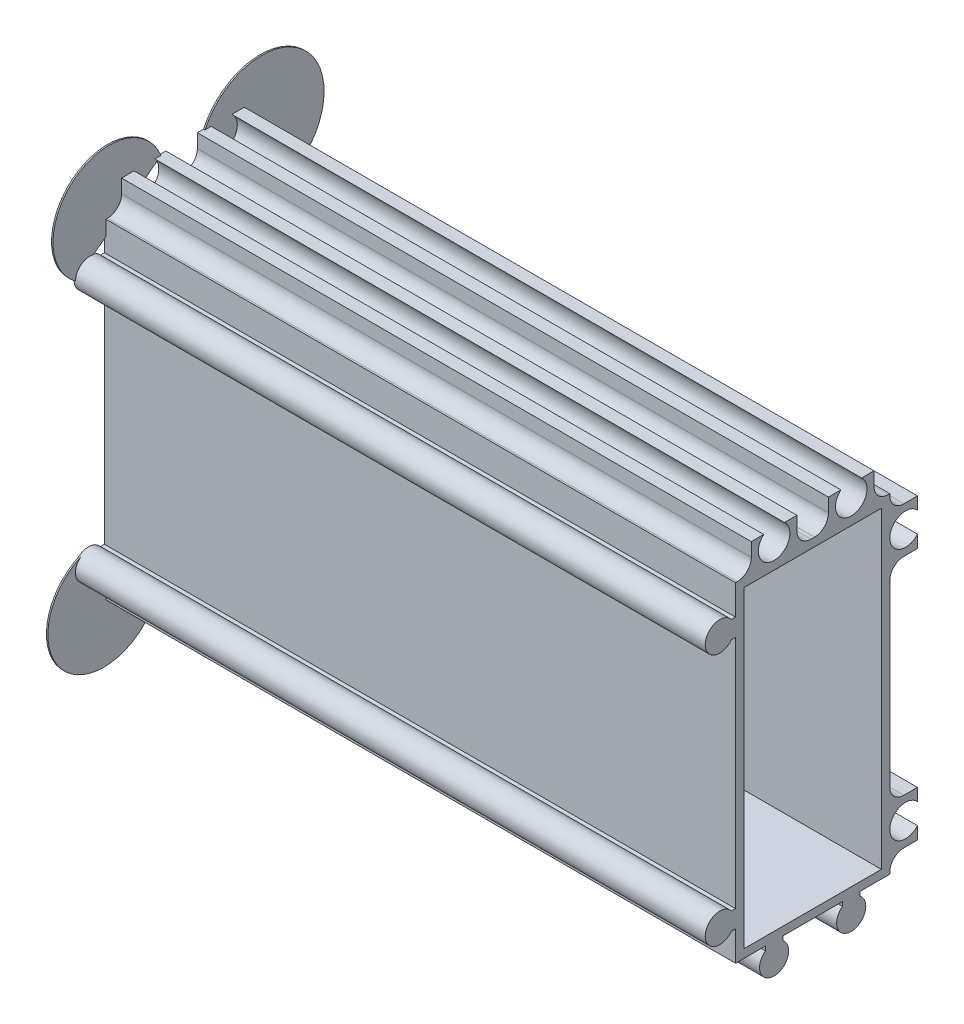
SolidWorks part; units mm, degrees
ref_plane "Спереди" through (0, 0, 0) normal (0, 0, 1) x (1, 0, 0)
ref_plane "Сверху" through (0, 0, 0) normal (0, 1, 0) x (1, 0, 0)
ref_plane "Справа" through (0, 0, 0) normal (1, 0, 0) x (0, 0, -1)
ref_plane "Плоскость4" through (90, 0, 0) normal (1, 0, 0) x (0, 0, -1)
sketch "Эскиз1" plane through (90, 0, 0) normal (1, 0, 0) x (0, 0, -1)
  line L0 (6.75, -24.0938) -> (6.75, 19.25)
  line L1 (6.75, 19.25) -> (-11.5938, 19.25)
  line L2 (-11.5938, 16.75) -> (-11, 16.75)
  line L3 (-11, 16.75) -> (-11, -16.75)
  line L4 (-11, -16.75) -> (-11.5938, -16.75)
  line L5 (-11.5938, -19.25) -> (-11, -19.25)
  line L6 (-11, -19.25) -> (-11, -23.5)
  line L7 (-11, -23.5) -> (-6.75, -23.5)
  line L8 (-6.75, -23.5) -> (-6.75, -24.0938)
  line L9 (-4.25, -24.0938) -> (-4.25, -23.5)
  line L10 (-4.25, -23.5) -> (4.25, -23.5)
  line L11 (4.25, -23.5) -> (4.25, -24.0938)
  arc A0 (-11.5938, 19.25) -> (-11.5938, 16.75) centre (-13.25, 18) ccw
  arc A1 (-11.5938, -16.75) -> (-11.5938, -19.25) centre (-13.25, -18) ccw
  arc A2 (-6.75, -24.0938) -> (-4.25, -24.0938) centre (-5.5, -25.75) ccw
  arc A3 (4.25, -24.0938) -> (6.75, -24.0938) centre (5.5, -25.75) ccw
extrude "Бобышка-Вытянуть1" add sketch "Эскиз1" against normal blind 90
sketch "Эскиз2" plane through (0, 19.25, 0) normal (0, 1, 0) x (-1, 0, 0)
  line L0 (-90, -6.75) -> (-90, 11)
  line L1 (-90, 11) -> (0, 11)
  line L2 (0, 11) -> (0, -6.75)
  line L3 (0, -6.75) -> (-90, -6.75)
extrude "Бобышка-Вытянуть2" add sketch "Эскиз2" along normal blind 8.2
sketch "Эскиз3" plane through (0, 0, -6.75) normal (0, 0, -1) x (-1, 0, 0)
  line L0 (0, -23.5) -> (-90, -23.5)
  line L1 (-90, -23.5) -> (-90, 27.45)
  line L2 (-90, 27.45) -> (0, 27.45)
  line L3 (0, 27.45) -> (0, -23.5)
extrude "Бобышка-Вытянуть3" add sketch "Эскиз3" along normal blind 8.2
sketch "Эскиз4" plane through (0, 0, 0) normal (-1, 0, 0) x (0, 0, 1)
  line L0 (-14.95, -14.75) -> (-11, -14.75)
  line L1 (-11, -14.75) -> (-11, 14.75)
  line L2 (-11, 14.75) -> (-14.95, 14.75)
  line L3 (-14.95, 14.75) -> (-14.95, -14.75)
extrude "Вырез-Вытянуть1" cut sketch "Эскиз4" against normal through all
sketch "Эскиз5" plane through (0, 0, 0) normal (-1, 0, 0) x (0, 0, 1)
  line L0 (-14.95, 27.45) -> (-14.95, 21.25)
  line L1 (-14.95, 21.25) -> (-11, 21.25)
  line L2 (-11, 21.25) -> (-11, 27.45)
  line L3 (-11, 27.45) -> (-14.95, 27.45)
extrude "Вырез-Вытянуть2" cut sketch "Эскиз5" against normal through all
sketch "Эскиз6" plane through (0, 0, 0) normal (-1, 0, 0) x (0, 0, 1)
  line L0 (-11, 27.45) -> (-11, 23.5)
  line L1 (-11, 23.5) -> (-8.75, 23.5)
  line L2 (-8.75, 23.5) -> (-8.75, 27.45)
  line L3 (-8.75, 27.45) -> (-11, 27.45)
extrude "Вырез-Вытянуть3" cut sketch "Эскиз6" against normal through all
sketch "Эскиз7" plane through (0, 0, 0) normal (-1, 0, 0) x (0, 0, 1)
  line L0 (-2.25, 27.45) -> (-2.25, 23.5)
  line L1 (-2.25, 23.5) -> (2.25, 23.5)
  line L2 (2.25, 23.5) -> (2.25, 27.45)
  line L3 (2.25, 27.45) -> (-2.25, 27.45)
extrude "Вырез-Вытянуть4" cut sketch "Эскиз7" against normal through all
sketch "Эскиз8" plane through (0, 0, 0) normal (-1, 0, 0) x (0, 0, 1)
  line L0 (11, 27.45) -> (8.75, 27.45)
  line L1 (8.75, 27.45) -> (8.75, 23.5)
  line L2 (8.75, 23.5) -> (11, 23.5)
  line L3 (11, 23.5) -> (11, 27.45)
extrude "Вырез-Вытянуть5" cut sketch "Эскиз8" against normal through all
sketch "Эскиз9" plane through (0, 0, 0) normal (-1, 0, 0) x (0, 0, 1)
  line L0 (-14.95, -23.5) -> (-11, -23.5)
  line L1 (-11, -23.5) -> (-11, -21.25)
  line L2 (-11, -21.25) -> (-14.95, -21.25)
  line L3 (-14.95, -21.25) -> (-14.95, -23.5)
extrude "Вырез-Вытянуть6" cut sketch "Эскиз9" against normal through all
sketch "Эскиз10" plane through (90, 0, 0) normal (1, 0, 0) x (0, 0, -1)
  line L0 (9.8, 22.3) -> (-9.8, 22.3)
  line L1 (-9.8, 22.3) -> (-9.8, -22.3)
  line L2 (-9.8, -22.3) -> (9.8, -22.3)
  line L3 (9.8, -22.3) -> (9.8, 22.3)
  line L4 (-11, 16.75) -> (-11, -16.75) construction
  line L8 (11, -14.75) -> (11, 14.75) construction
  line L9 (2.25, 23.5) -> (-2.25, 23.5) construction
  line L10 (-4.25, -23.5) -> (4.25, -23.5) construction
  dimension "D1" = 1.2
  dimension "D2" = 1.2
  dimension "D3" = 1.2
  dimension "D4" = 1.2
extrude "Вырез-Вытянуть7" cut sketch "Эскиз10" against normal blind 86.2
hole_wizard "Диаметр отверстия Ø2.5 (2.5)1" positions "Эскиз12" profile "Эскиз11" hole size "Ø2.5" standard "Ansi Metric"
sketch "Эскиз12" plane through (90, 0, 0) normal (1, 0, 0) x (0, 0, -1)
  point P0 (5.5, -25.75)
  point P1 (-13.25, -18)
  point P2 (-5.5, -25.75)
  point P3 (-13.25, 18)
sketch "Эскиз11" plane through (90, -25.75, -5.5) normal (0, 1, 0) x (0, 0, -1)
  line L0 (0, 0) -> (0, 90)
  line L1 (0, 90) -> (1.25, 90)
  line L2 (1.25, 90) -> (1.25, 0)
  line L5 (1.25, 0) -> (0, 0)
  line L11 (0, -6.35) -> (0, 107.95) construction
  dimension "Диаметр сквозного отверстия" = 2.5
  dimension "Глубина сквозного отверстия" = 90
hole_wizard "Диаметр отверстия Ø4.5 (4.5)1" positions "Эскиз14" profile "Эскиз13" hole size "Ø4.5" standard "Ansi Metric"
sketch "Эскиз14" plane through (0, 0, 0) normal (-1, 0, 0) x (0, 0, 1)
  point P0 (-13.25, -18)
  point P1 (-13.25, 18)
  point P2 (-5.5, 25.75)
  point P3 (5.5, 25.75)
sketch "Эскиз13" plane through (0, -18, -13.25) normal (0, 1, 0) x (0, 0, 1)
  line L0 (0, 0) -> (0, 90)
  line L1 (0, 90) -> (2.25, 90)
  line L2 (2.25, 90) -> (2.25, 0)
  line L5 (2.25, 0) -> (0, 0)
  line L11 (0, -6.35) -> (0, 107.95) construction
  dimension "Диаметр сквозного отверстия" = 4.5
  dimension "Глубина сквозного отверстия" = 90
hole_wizard "Диаметр отверстия Ø8.3 (8.3)1" [suppressed] positions "Эскиз16" profile "Эскиз15" hole size "Ø8.3" standard "Ansi Metric"
sketch "Эскиз16" plane through (0, 0, 0) normal (-1, 0, 0) x (0, 0, 1)
  point P0 (0, 0)
sketch "Эскиз15" plane through (0, 0, 0) normal (0, 1, 0) x (0, 0, 1)
  line L0 (0, 0) -> (0, 3.2)
  line L1 (0, 3.2) -> (4.15, 3.2)
  line L2 (4.15, 3.2) -> (4.15, 0)
  line L5 (4.15, 0) -> (0, 0)
  line L10 (0, 3.2) -> (-4.15, 3.2) construction
  line L11 (0, -6.35) -> (0, 107.95) construction
  dimension "Диаметр отверстия" = 8.3
  dimension "Глубина отверстия" = 3.2
  dimension "Угол заточки сверла" = 180
fillet "Скругление1" radius 2 1 edges at (45, 23.5, 8.75)
fillet "Скругление2" radius 2 7 edges at (45, -21.25, -11) (45, -14.75, -11) (45, 14.75, -11) (45, 21.25, -11) (45, 23.5, -8.75) (45, 23.5, -2.25) (45, 23.5, 2.25)
sketch "Эскиз17" plane through (90, 0, 0) normal (1, 0, 0) x (0, 0, -1)
  circle A0 centre (5.5, -25.75) radius 1.25 construction
  circle A1 centre (-5.5, -25.75) radius 1.25 construction
  circle A2 centre (-13.25, -18) radius 1.25 construction
  circle A3 centre (-13.25, 18) radius 1.25 construction
  circle A4 centre (5.5, -25.75) radius 1.25
  circle A5 centre (-5.5, -25.75) radius 1.25
  circle A6 centre (-13.25, -18) radius 1.25
  circle A7 centre (-13.25, 18) radius 1.25
extrude "Бобышка-Вытянуть4" add sketch "Эскиз17" against normal blind 90
sketch "Эскиз18" [suppressed] plane through (0, 0, 0) normal (-1, 0, 0) x (0, 0, 1)
  circle A0 centre (0, 0) radius 4.15 construction
  circle A1 centre (0, 0) radius 4.15
extrude "Вырез-Вытянуть8" [suppressed] cut sketch "Эскиз18" against normal blind 100
sketch "Эскиз19" plane through (0, 0, 0) normal (-1, 0, 0) x (0, 0, 1)
  line L0 (11, -23.5) -> (-11, 23.25) construction
  line L1 (-11, -23.5) -> (11, 23.5157) construction
  line L2 (11, 23.5) -> (11, 19.25) construction
  line L3 (0, 0) -> (11, 0) construction
  line L4 (11, 16.75) -> (11, -16.75) construction
  line L5 (-4.0261, 27.45) -> (-2.25, 27.45) construction
  line L6 (-14.95, 14.75) -> (-14.95, 16.5261) construction
  line L7 (2.25, 27.45) -> (4.0261, 27.45) construction
  line L8 (-14.95, -16.5261) -> (-14.95, -14.75) construction
  line L9 (-14.95, 15.638) -> (-3.138, 27.45)
  line L10 (15.325, 18) -> (3.138, 27.45)
  line L11 (14.6082, -16.4313) -> (4.1213, -27.3007)
  line L12 (-5.5, -27.825) -> (-14.95, -15.638)
  arc A0 (-3.138, 27.45) -> (-14.95, 15.638) centre (-11.2222, 23.7222) ccw
  arc A1 (15.325, 18) -> (3.138, 27.45) centre (10.5377, 24.4095) ccw
  arc A2 (8.75, 25.5) -> (10.75, 23.5) centre (10.75, 25.5) ccw construction
  arc A3 (11.5938, 16.75) -> (11.5938, 19.25) centre (13.25, 18) ccw construction
  arc A4 (-14.95, -15.638) -> (-5.5, -27.825) centre (-11.9095, -23.0377) ccw
  arc A5 (-6.75, -24.0938) -> (-4.25, -24.0938) centre (-5.5, -25.75) ccw construction
  arc A6 (14.6082, -16.4313) -> (4.1213, -27.3007) centre (11.2647, -23.6991) cw
  arc A9 (11.5938, -19.25) -> (11.5938, -16.75) centre (13.25, -18) ccw construction
  arc A10 (4.25, -24.0938) -> (6.75, -24.0938) centre (5.5, -25.75) ccw construction
  point P34 (14.6224, -16.4437)
  point P44 (4.2527, -27.4082)
  point P51 (14.953, -16.8144)
  point P52 (14.6082, -16.4313)
  point P53 (4.1213, -27.3007)
  dimension "D1" = 8.9023
  dimension "D2" = 8
  dimension "D3" = 8
  dimension "D4" = 8
extrude "Бобышка-Вытянуть5" add sketch "Эскиз19" against normal blind 0.2
equation "\"D2@Эскиз10\"=\"D1@Эскиз10\""
equation "\"D3@Эскиз10\"=\"D1@Эскиз10\""
equation "\"D4@Эскиз10\"=\"D1@Эскиз10\""
